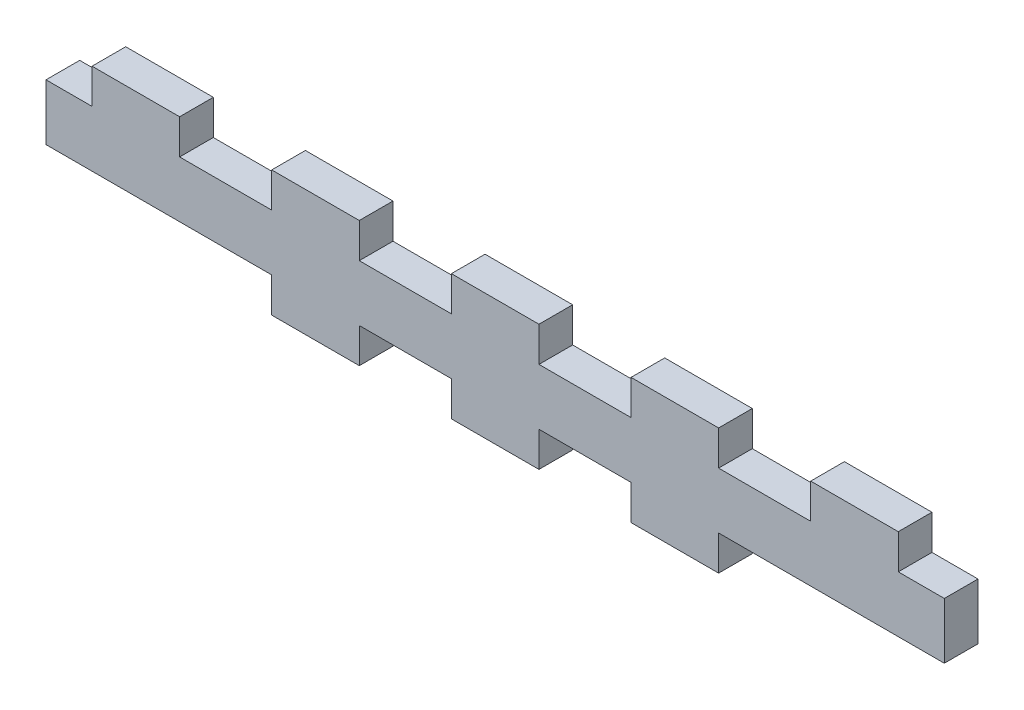
SolidWorks part; units mm, degrees
ref_plane "Front Plane" through (0, 0, 0) normal (0, 0, 1) x (1, 0, 0)
ref_plane "Top Plane" through (0, 0, 0) normal (0, 1, 0) x (1, 0, 0)
ref_plane "Right Plane" through (0, 0, 0) normal (1, 0, 0) x (0, 0, -1)
sketch "Sketch1" plane through (0, 0, 0) normal (0, 0, 1) x (1, 0, 0)
  line L1 (0, 0) -> (80, 0)
  line L2 (0, 0) -> (0, -11.2)
  line L3 (0, -11.2) -> (80, -11.2)
  line L4 (80, 0) -> (80, -11.2)
sketch "Sketch2" plane through (0, 0, 0) normal (1, 0, 0) x (0, 0, -1)
  line L1 (0, 0) -> (-3, 0)
  line L2 (0, 0) -> (0, -11.2)
  line L3 (0, -11.2) -> (-3, -11.2)
  line L4 (-3, 0) -> (-3, -11.2)
extrude "Boss-Extrude1" add sketch "Sketch1" along normal up to vertex (3 mm away) up to point (0, -11.2, 3)
sketch "Sketch3" plane through (0, 0, 0) normal (0, 0, 1) x (1, 0, 0)
  line L4 (0, -11.2) -> (4, -11.2)
  line L5 (0, -8.2) -> (0, -11.2)
  line L6 (4, -8.2) -> (0, -8.2)
  line L7 (4, -11.2) -> (4, -8.2)
  line L8 (0, -11.2) -> (4, -11.2) construction
  line L9 (0, -8.2) -> (0, -11.2) construction
  line L10 (4, -8.2) -> (0, -8.2) construction
  line L11 (4, -11.2) -> (4, -8.2) construction
  line L12 (0, -3) -> (4, -3)
  line L13 (0, 0) -> (0, -3)
  line L14 (4, 0) -> (0, 0)
  line L15 (4, -3) -> (4, 0)
  line L16 (0, -3) -> (4, -3) construction
  line L17 (0, 0) -> (0, -3) construction
  line L18 (4, 0) -> (0, 0) construction
  line L19 (4, -3) -> (4, 0) construction
  line L20 (20, -8.2) -> (12, -8.2)
  line L21 (20, -11.2) -> (20, -8.2)
  line L22 (12, -11.2) -> (20, -11.2)
  line L23 (12, -8.2) -> (12, -11.2)
  line L24 (20, -8.2) -> (12, -8.2) construction
  line L25 (20, -11.2) -> (20, -8.2) construction
  line L26 (12, -11.2) -> (20, -11.2) construction
  line L27 (12, -8.2) -> (12, -11.2) construction
  line L28 (36, 0) -> (28, 0)
  line L29 (36, -3) -> (36, 0)
  line L30 (28, -3) -> (36, -3)
  line L31 (28, 0) -> (28, -3)
  line L32 (36, 0) -> (28, 0) construction
  line L33 (36, -3) -> (36, 0) construction
  line L34 (28, -3) -> (36, -3) construction
  line L35 (28, 0) -> (28, -3) construction
  line L36 (20, 0) -> (12, 0)
  line L37 (20, -3) -> (20, 0)
  line L38 (12, -3) -> (20, -3)
  line L39 (12, 0) -> (12, -3)
  line L40 (20, 0) -> (12, 0) construction
  line L41 (20, -3) -> (20, 0) construction
  line L42 (12, -3) -> (20, -3) construction
  line L43 (12, 0) -> (12, -3) construction
  line L44 (44, -8.2) -> (44, -11.2)
  line L45 (44, -11.2) -> (52, -11.2)
  line L46 (52, -11.2) -> (52, -8.2)
  line L47 (52, -8.2) -> (44, -8.2)
  line L48 (44, -8.2) -> (44, -11.2) construction
  line L49 (44, -11.2) -> (52, -11.2) construction
  line L50 (52, -11.2) -> (52, -8.2) construction
  line L51 (52, -8.2) -> (44, -8.2) construction
  line L52 (36, -8.2) -> (28, -8.2)
  line L53 (36, -11.2) -> (36, -8.2)
  line L54 (28, -11.2) -> (36, -11.2)
  line L55 (28, -8.2) -> (28, -11.2)
  line L56 (36, -8.2) -> (28, -8.2) construction
  line L57 (36, -11.2) -> (36, -8.2) construction
  line L58 (28, -11.2) -> (36, -11.2) construction
  line L59 (28, -8.2) -> (28, -11.2) construction
  line L60 (80, -11.2) -> (80, -8.2)
  line L61 (80, -8.2) -> (76, -8.2)
  line L62 (76, -8.2) -> (76, -11.2)
  line L63 (76, -11.2) -> (80, -11.2)
  line L64 (80, -11.2) -> (80, -8.2) construction
  line L65 (80, -8.2) -> (76, -8.2) construction
  line L66 (76, -8.2) -> (76, -11.2) construction
  line L67 (76, -11.2) -> (80, -11.2) construction
  line L68 (60, 0) -> (60, -3)
  line L69 (60, -3) -> (68, -3)
  line L70 (68, -3) -> (68, 0)
  line L71 (68, 0) -> (60, 0)
  line L72 (60, 0) -> (60, -3) construction
  line L73 (60, -3) -> (68, -3) construction
  line L74 (68, -3) -> (68, 0) construction
  line L75 (68, 0) -> (60, 0) construction
  line L76 (44, 0) -> (44, -3)
  line L77 (44, -3) -> (52, -3)
  line L78 (52, -3) -> (52, 0)
  line L79 (52, 0) -> (44, 0)
  line L80 (44, 0) -> (44, -3) construction
  line L81 (44, -3) -> (52, -3) construction
  line L82 (52, -3) -> (52, 0) construction
  line L83 (52, 0) -> (44, 0) construction
  line L84 (68, -11.2) -> (68, -8.2)
  line L85 (60, -11.2) -> (68, -11.2)
  line L86 (60, -8.2) -> (60, -11.2)
  line L87 (68, -8.2) -> (60, -8.2)
  line L88 (68, -11.2) -> (68, -8.2) construction
  line L89 (60, -11.2) -> (68, -11.2) construction
  line L90 (60, -8.2) -> (60, -11.2) construction
  line L91 (68, -8.2) -> (60, -8.2) construction
  line L92 (76, 0) -> (76, -3)
  line L93 (80, 0) -> (76, 0)
  line L94 (80, -3) -> (80, 0)
  line L95 (76, -3) -> (80, -3)
  line L96 (76, 0) -> (76, -3) construction
  line L97 (80, 0) -> (76, 0) construction
  line L98 (80, -3) -> (80, 0) construction
  line L99 (76, -3) -> (80, -3) construction
  line L144 (-0.1, -11.3) -> (20.1, -11.3)
  line L146 (20.1, -8.1) -> (-0.1, -8.1)
  line L147 (-0.1, -8.1) -> (-0.1, -11.3)
  line L148 (-0.1, -3.1) -> (4.1, -3.1)
  line L149 (4.1, -3.1) -> (4.1, 0.1)
  line L150 (4.1, 0.1) -> (-0.1, 0.1)
  line L151 (-0.1, 0.1) -> (-0.1, -3.1)
  line L153 (4.1, -8.1) -> (-0.1, -8.1) construction
  line L154 (-0.1, -11.3) -> (4.1, -11.3) construction
  line L155 (20.1, -11.3) -> (20.1, -8.1)
  line L156 (36.1, 0.1) -> (27.9, 0.1)
  line L157 (27.9, 0.1) -> (27.9, -3.1)
  line L158 (27.9, -3.1) -> (36.1, -3.1)
  line L159 (36.1, -3.1) -> (36.1, 0.1)
  line L160 (20.1, 0.1) -> (11.9, 0.1)
  line L161 (11.9, 0.1) -> (11.9, -3.1)
  line L162 (11.9, -3.1) -> (20.1, -3.1)
  line L163 (20.1, -3.1) -> (20.1, 0.1)
  line L164 (43.9, -8.1) -> (43.9, -11.3)
  line L165 (43.9, -11.3) -> (52.1, -11.3)
  line L166 (52.1, -11.3) -> (52.1, -8.1)
  line L167 (52.1, -8.1) -> (43.9, -8.1)
  line L168 (36.1, -8.1) -> (27.9, -8.1)
  line L169 (27.9, -8.1) -> (27.9, -11.3)
  line L170 (27.9, -11.3) -> (36.1, -11.3)
  line L171 (36.1, -11.3) -> (36.1, -8.1)
  line L172 (80.1, -11.3) -> (80.1, -8.1)
  line L173 (80.1, -8.1) -> (59.9, -8.1)
  line L174 (80.1, -8.1) -> (75.9, -8.1) construction
  line L175 (59.9, -11.3) -> (80.1, -11.3)
  line L176 (59.9, 0.1) -> (59.9, -3.1)
  line L177 (59.9, -3.1) -> (68.1, -3.1)
  line L178 (68.1, -3.1) -> (68.1, 0.1)
  line L179 (68.1, 0.1) -> (59.9, 0.1)
  line L180 (43.9, 0.1) -> (43.9, -3.1)
  line L181 (43.9, -3.1) -> (52.1, -3.1)
  line L182 (52.1, -3.1) -> (52.1, 0.1)
  line L183 (52.1, 0.1) -> (43.9, 0.1)
  line L184 (75.9, -11.3) -> (80.1, -11.3) construction
  line L186 (59.9, -8.1) -> (59.9, -11.3)
  line L188 (75.9, 0.1) -> (75.9, -3.1)
  line L189 (75.9, -3.1) -> (80.1, -3.1)
  line L190 (80.1, -3.1) -> (80.1, 0.1)
  line L191 (80.1, 0.1) -> (75.9, 0.1)
  line L384 (4.1, -11.3) -> (4.1, -8.1) construction
  line L385 (11.9, -8.1) -> (11.9, -11.3) construction
  line L386 (20.1, -8.1) -> (11.9, -8.1) construction
  line L387 (11.9, -11.3) -> (20.1, -11.3) construction
  line L388 (68.1, -11.3) -> (68.1, -8.1) construction
  line L389 (68.1, -8.1) -> (59.9, -8.1) construction
  line L390 (59.9, -11.3) -> (68.1, -11.3) construction
  line L391 (75.9, -8.1) -> (75.9, -11.3) construction
  dimension "D1" = 0
  dimension "D2" = 0
  dimension "D3" = 0
  dimension "D4" = 0
  dimension "D5" = 0
  dimension "D6" = 0
  dimension "D7" = 0
  dimension "D8" = 0
  dimension "D9" = 0
  dimension "D10" = 0
  dimension "D11" = 0
  dimension "D12" = 0
  dimension "D13" = 0.1
extrude "Cut-Extrude1" cut sketch "Sketch3" along normal through all
